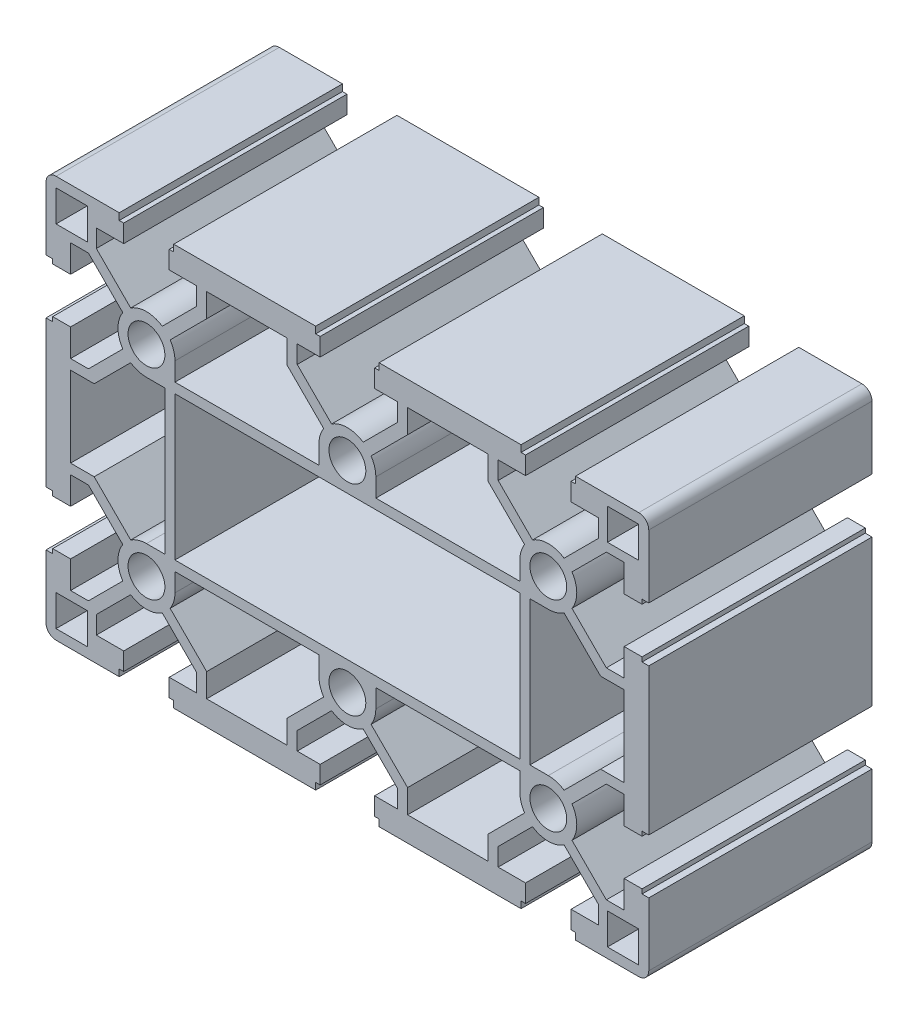
SolidWorks part; units mm, degrees
material "6063-T5"
ref_plane "Ön Düzlem" through (0, 0, 0) normal (0, 0, 1) x (1, 0, 0)
ref_plane "Üst Düzlem" through (0, 0, 0) normal (0, 1, 0) x (1, 0, 0)
ref_plane "Sağ Düzlem" through (0, 0, 0) normal (1, 0, 0) x (0, 0, -1)
sketch "Çizim1" plane through (0, 0, 0) normal (0, 0, 1) x (1, 0, 0)
  line L0 (0, -1000) -> (0, 49000) construction
  line L1 (51.1, 45) -> (65.25, 45)
  line L2 (67.5, 42.75) -> (67.5, 28.6)
  line L3 (67.5, 28.6) -> (66, 28.6)
  line L4 (66, 28.6) -> (66, 27.6)
  line L5 (66, 27.6) -> (62, 27.6)
  line L6 (62, 27.6) -> (62, 33.7322)
  line L7 (-1000, 0) -> (49000, 0) construction
  line L8 (45, -1000) -> (45, 49000) construction
  line L9 (-45, -1000) -> (-45, 49000) construction
  line L10 (-1000, -22.5) -> (49000, -22.5) construction
  line L11 (-1000, 22.5) -> (49000, 22.5) construction
  line L12 (62, 33.7322) -> (58, 33.7322)
  line L13 (45, 22.5) -> (99.0284, 76.5284) construction
  line L14 (50.3042, 26.0364) -> (58, 33.7322)
  line L15 (56.2322, 39.5) -> (56.2322, 35.5)
  line L16 (-45, -18.375) -> (-40.875, -18.375) construction
  line L17 (65.25, 42.75) -> (58.25, 42.75)
  line L18 (65.25, 42.75) -> (65.25, 35.75)
  line L19 (65.25, 35.75) -> (58.25, 35.75)
  line L20 (58.25, 42.75) -> (58.25, 35.75)
  line L21 (48.5364, 27.8042) -> (56.2322, 35.5)
  line L22 (51.1, 45) -> (51.1, 43.5)
  line L23 (51.1, 43.5) -> (50.1, 43.5)
  line L24 (50.1, 43.5) -> (50.1, 39.5)
  line L25 (50.1, 39.5) -> (56.2322, 39.5)
  line L26 (50.3042, 18.9636) -> (58, 11.2678)
  line L27 (62, 11.2678) -> (58, 11.2678)
  line L28 (62, 17.4) -> (62, 11.2678)
  line L29 (66, 17.4) -> (62, 17.4)
  line L30 (66, 16.4) -> (66, 17.4)
  line L31 (67.5, 16.4) -> (66, 16.4)
  line L32 (67.5, -16.4) -> (67.5, 16.4)
  line L33 (-40.875, 22.5) -> (-40.875, 18.375) construction
  line L34 (56.7145, 9.0178) -> (62, 9.0178)
  line L35 (62, 9.0178) -> (62, -9.0178)
  line L36 (48.5364, 17.1958) -> (56.7145, 9.0178)
  line L37 (45, 22.5) -> (11.8849, 55.6151) construction
  line L38 (31.5178, 39.5) -> (13.4822, 39.5)
  line L39 (31.5178, 34.2145) -> (31.5178, 39.5)
  line L40 (39.6958, 26.0364) -> (31.5178, 34.2145)
  line L41 (41.4636, 27.8042) -> (33.7678, 35.5)
  line L42 (33.7678, 39.5) -> (33.7678, 35.5)
  line L43 (39.9, 39.5) -> (33.7678, 39.5)
  line L44 (39.9, 43.5) -> (39.9, 39.5)
  line L45 (38.9, 43.5) -> (39.9, 43.5)
  line L46 (38.9, 45) -> (38.9, 43.5)
  line L47 (7.1, 45) -> (38.9, 45)
  line L48 (22.5, -1000) -> (22.5, 49000) construction
  line L49 (-22.5, -1000) -> (-22.5, 49000) construction
  line L50 (38.625, 22.5) -> (38.625, 18.375)
  line L51 (45, 16.125) -> (40.875, 16.125)
  line L52 (45, 18.375) -> (40.875, 18.375) construction
  line L53 (40.875, 22.5) -> (40.875, 18.375) construction
  line L54 (38.625, 18.375) -> (6.375, 18.375)
  line L55 (38.625, 16.125) -> (38.625, -16.125)
  line L56 (38.625, 16.125) -> (-38.625, 16.125)
  line L57 (40.875, 16.125) -> (40.875, -16.125)
  line L58 (13.4822, 34.2145) -> (13.4822, 39.5)
  line L59 (5.3042, 26.0364) -> (13.4822, 34.2145)
  line L60 (6.375, 22.5) -> (6.375, 18.375)
  line L61 (0, 22.5) -> (33.1151, 55.6151) construction
  line L62 (7.1, 43.5) -> (7.1, 45)
  line L63 (7.1, 43.5) -> (6.1, 43.5)
  line L64 (6.1, 43.5) -> (6.1, 39.5)
  line L65 (6.1, 39.5) -> (11.2322, 39.5)
  line L66 (11.2322, 39.5) -> (11.2322, 35.5)
  line L67 (3.5364, 27.8042) -> (11.2322, 35.5)
  line L68 (40.875, -22.5) -> (40.875, -18.375) construction
  line L69 (-45, 18.375) -> (-40.875, 18.375) construction
  line L70 (-3.5364, 27.8042) -> (-11.2322, 35.5)
  line L71 (-11.2322, 39.5) -> (-11.2322, 35.5)
  line L72 (-6.1, 39.5) -> (-11.2322, 39.5)
  line L73 (-6.1, 43.5) -> (-6.1, 39.5)
  line L74 (-7.1, 43.5) -> (-6.1, 43.5)
  line L75 (-7.1, 45) -> (-7.1, 43.5)
  line L76 (-6.375, 22.5) -> (-6.375, 18.375)
  line L77 (-5.3042, 26.0364) -> (-13.4822, 34.2145)
  line L78 (-13.4822, 34.2145) -> (-13.4822, 39.5)
  line L79 (-40.875, 16.125) -> (-40.875, -16.125)
  line L80 (-38.625, 16.125) -> (-38.625, -16.125)
  line L81 (-38.625, 18.375) -> (-6.375, 18.375)
  line L82 (-45, 16.125) -> (-40.875, 16.125)
  line L83 (-38.625, 22.5) -> (-38.625, 18.375)
  line L84 (-7.1, 45) -> (-38.9, 45)
  line L85 (-38.9, 45) -> (-38.9, 43.5)
  line L86 (-38.9, 43.5) -> (-39.9, 43.5)
  line L87 (-39.9, 43.5) -> (-39.9, 39.5)
  line L88 (-39.9, 39.5) -> (-33.7678, 39.5)
  line L89 (-33.7678, 39.5) -> (-33.7678, 35.5)
  line L90 (-41.4636, 27.8042) -> (-33.7678, 35.5)
  line L91 (-39.6958, 26.0364) -> (-31.5178, 34.2145)
  line L92 (-31.5178, 34.2145) -> (-31.5178, 39.5)
  line L93 (-31.5178, 39.5) -> (-13.4822, 39.5)
  line L94 (-48.5364, 17.1958) -> (-56.7145, 9.0178)
  line L95 (-62, 9.0178) -> (-62, -9.0178)
  line L96 (-56.7145, 9.0178) -> (-62, 9.0178)
  line L97 (-67.5, -16.4) -> (-67.5, 16.4)
  line L98 (-67.5, 16.4) -> (-66, 16.4)
  line L99 (-66, 16.4) -> (-66, 17.4)
  line L100 (-66, 17.4) -> (-62, 17.4)
  line L101 (-62, 17.4) -> (-62, 11.2678)
  line L102 (-62, 11.2678) -> (-58, 11.2678)
  line L103 (-50.3042, 18.9636) -> (-58, 11.2678)
  line L104 (-50.1, 39.5) -> (-56.2322, 39.5)
  line L105 (-50.1, 43.5) -> (-50.1, 39.5)
  line L106 (-51.1, 43.5) -> (-50.1, 43.5)
  line L107 (-51.1, 45) -> (-51.1, 43.5)
  line L108 (-48.5364, 27.8042) -> (-56.2322, 35.5)
  line L109 (-58.25, 42.75) -> (-58.25, 35.75)
  line L110 (-65.25, 35.75) -> (-58.25, 35.75)
  line L111 (-65.25, 42.75) -> (-65.25, 35.75)
  line L112 (-65.25, 42.75) -> (-58.25, 42.75)
  line L113 (-56.2322, 39.5) -> (-56.2322, 35.5)
  line L114 (-50.3042, 26.0364) -> (-58, 33.7322)
  line L115 (-62, 33.7322) -> (-58, 33.7322)
  line L116 (-62, 27.6) -> (-62, 33.7322)
  line L117 (-66, 27.6) -> (-62, 27.6)
  line L118 (-66, 28.6) -> (-66, 27.6)
  line L119 (-67.5, 28.6) -> (-66, 28.6)
  line L120 (-67.5, 42.75) -> (-67.5, 28.6)
  line L121 (-51.1, 45) -> (-65.25, 45)
  line L122 (45, -18.375) -> (40.875, -18.375) construction
  line L123 (-40.875, -22.5) -> (-40.875, -18.375) construction
  line L124 (-51.1, -45) -> (-65.25, -45)
  line L125 (-67.5, -42.75) -> (-67.5, -28.6)
  line L126 (-67.5, -28.6) -> (-66, -28.6)
  line L127 (-66, -28.6) -> (-66, -27.6)
  line L128 (-66, -27.6) -> (-62, -27.6)
  line L129 (-62, -27.6) -> (-62, -33.7322)
  line L130 (-62, -33.7322) -> (-58, -33.7322)
  line L131 (-50.3042, -26.0364) -> (-58, -33.7322)
  line L132 (-56.2322, -39.5) -> (-56.2322, -35.5)
  line L133 (-65.25, -42.75) -> (-58.25, -42.75)
  line L134 (-65.25, -42.75) -> (-65.25, -35.75)
  line L135 (-65.25, -35.75) -> (-58.25, -35.75)
  line L136 (-58.25, -42.75) -> (-58.25, -35.75)
  line L137 (-48.5364, -27.8042) -> (-56.2322, -35.5)
  line L138 (-51.1, -45) -> (-51.1, -43.5)
  line L139 (-51.1, -43.5) -> (-50.1, -43.5)
  line L140 (-50.1, -43.5) -> (-50.1, -39.5)
  line L141 (-50.1, -39.5) -> (-56.2322, -39.5)
  line L142 (-50.3042, -18.9636) -> (-58, -11.2678)
  line L143 (-62, -11.2678) -> (-58, -11.2678)
  line L144 (-62, -17.4) -> (-62, -11.2678)
  line L145 (-66, -17.4) -> (-62, -17.4)
  line L146 (-66, -16.4) -> (-66, -17.4)
  line L147 (-67.5, -16.4) -> (-66, -16.4)
  line L148 (-56.7145, -9.0178) -> (-62, -9.0178)
  line L149 (-48.5364, -17.1958) -> (-56.7145, -9.0178)
  line L150 (-31.5178, -39.5) -> (-13.4822, -39.5)
  line L151 (-31.5178, -34.2145) -> (-31.5178, -39.5)
  line L152 (-39.6958, -26.0364) -> (-31.5178, -34.2145)
  line L153 (-41.4636, -27.8042) -> (-33.7678, -35.5)
  line L154 (-33.7678, -39.5) -> (-33.7678, -35.5)
  line L155 (-39.9, -39.5) -> (-33.7678, -39.5)
  line L156 (-39.9, -43.5) -> (-39.9, -39.5)
  line L157 (-38.9, -43.5) -> (-39.9, -43.5)
  line L158 (-38.9, -45) -> (-38.9, -43.5)
  line L159 (-7.1, -45) -> (-38.9, -45)
  line L160 (-38.625, -22.5) -> (-38.625, -18.375)
  line L161 (-45, -16.125) -> (-40.875, -16.125)
  line L162 (-38.625, -18.375) -> (-6.375, -18.375)
  line L163 (-13.4822, -34.2145) -> (-13.4822, -39.5)
  line L164 (-5.3042, -26.0364) -> (-13.4822, -34.2145)
  line L165 (-6.375, -22.5) -> (-6.375, -18.375)
  line L166 (-7.1, -45) -> (-7.1, -43.5)
  line L167 (-7.1, -43.5) -> (-6.1, -43.5)
  line L168 (-6.1, -43.5) -> (-6.1, -39.5)
  line L169 (-6.1, -39.5) -> (-11.2322, -39.5)
  line L170 (-11.2322, -39.5) -> (-11.2322, -35.5)
  line L171 (-3.5364, -27.8042) -> (-11.2322, -35.5)
  line L172 (3.5364, -27.8042) -> (11.2322, -35.5)
  line L173 (11.2322, -39.5) -> (11.2322, -35.5)
  line L174 (6.1, -39.5) -> (11.2322, -39.5)
  line L175 (6.1, -43.5) -> (6.1, -39.5)
  line L176 (7.1, -43.5) -> (6.1, -43.5)
  line L177 (7.1, -45) -> (7.1, -43.5)
  line L178 (6.375, -22.5) -> (6.375, -18.375)
  line L179 (5.3042, -26.0364) -> (13.4822, -34.2145)
  line L180 (13.4822, -34.2145) -> (13.4822, -39.5)
  line L181 (38.625, -16.125) -> (-38.625, -16.125)
  line L182 (38.625, -18.375) -> (6.375, -18.375)
  line L183 (45, -16.125) -> (40.875, -16.125)
  line L184 (38.625, -22.5) -> (38.625, -18.375)
  line L185 (7.1, -45) -> (38.9, -45)
  line L186 (38.9, -45) -> (38.9, -43.5)
  line L187 (38.9, -43.5) -> (39.9, -43.5)
  line L188 (39.9, -43.5) -> (39.9, -39.5)
  line L189 (39.9, -39.5) -> (33.7678, -39.5)
  line L190 (33.7678, -39.5) -> (33.7678, -35.5)
  line L191 (41.4636, -27.8042) -> (33.7678, -35.5)
  line L192 (39.6958, -26.0364) -> (31.5178, -34.2145)
  line L193 (31.5178, -34.2145) -> (31.5178, -39.5)
  line L194 (31.5178, -39.5) -> (13.4822, -39.5)
  line L195 (48.5364, -17.1958) -> (56.7145, -9.0178)
  line L196 (56.7145, -9.0178) -> (62, -9.0178)
  line L197 (67.5, -16.4) -> (66, -16.4)
  line L198 (66, -16.4) -> (66, -17.4)
  line L199 (66, -17.4) -> (62, -17.4)
  line L200 (62, -17.4) -> (62, -11.2678)
  line L201 (62, -11.2678) -> (58, -11.2678)
  line L202 (50.3042, -18.9636) -> (58, -11.2678)
  line L203 (50.1, -39.5) -> (56.2322, -39.5)
  line L204 (50.1, -43.5) -> (50.1, -39.5)
  line L205 (51.1, -43.5) -> (50.1, -43.5)
  line L206 (51.1, -45) -> (51.1, -43.5)
  line L207 (48.5364, -27.8042) -> (56.2322, -35.5)
  line L208 (58.25, -42.75) -> (58.25, -35.75)
  line L209 (65.25, -35.75) -> (58.25, -35.75)
  line L210 (65.25, -42.75) -> (65.25, -35.75)
  line L211 (65.25, -42.75) -> (58.25, -42.75)
  line L212 (56.2322, -39.5) -> (56.2322, -35.5)
  line L213 (50.3042, -26.0364) -> (58, -33.7322)
  line L214 (62, -33.7322) -> (58, -33.7322)
  line L215 (62, -27.6) -> (62, -33.7322)
  line L216 (66, -27.6) -> (62, -27.6)
  line L217 (66, -28.6) -> (66, -27.6)
  line L218 (67.5, -28.6) -> (66, -28.6)
  line L219 (67.5, -42.75) -> (67.5, -28.6)
  line L220 (51.1, -45) -> (65.25, -45)
  arc A0 (39.6958, 26.0364) -> (38.625, 22.5) centre (45, 22.5) ccw
  circle A1 centre (45, 22.5) radius 4.125
  arc A2 (48.5364, 27.8042) -> (41.4636, 27.8042) centre (45, 22.5) ccw
  arc A3 (-39.6958, -26.0364) -> (-38.625, -22.5) centre (-45, -22.5) ccw
  arc A4 (50.3042, 18.9636) -> (50.3042, 26.0364) centre (45, 22.5) ccw
  arc A5 (45, 16.125) -> (48.5364, 17.1958) centre (45, 22.5) ccw
  arc A6 (5.3042, 26.0364) -> (6.375, 22.5) centre (0, 22.5) cw
  arc A7 (-3.5364, 27.8042) -> (3.5364, 27.8042) centre (0, 22.5) cw
  circle A8 centre (0, 22.5) radius 4.125
  arc A9 (65.25, 45) -> (67.5, 42.75) centre (65.25, 42.75) cw
  arc A10 (-65.25, 45) -> (-67.5, 42.75) centre (-65.25, 42.75) ccw
  arc A11 (-5.3042, 26.0364) -> (-6.375, 22.5) centre (0, 22.5) ccw
  arc A12 (-45, 16.125) -> (-48.5364, 17.1958) centre (-45, 22.5) cw
  arc A13 (-50.3042, 18.9636) -> (-50.3042, 26.0364) centre (-45, 22.5) cw
  arc A14 (-48.5364, 27.8042) -> (-41.4636, 27.8042) centre (-45, 22.5) cw
  circle A15 centre (-45, 22.5) radius 4.125
  arc A16 (-39.6958, 26.0364) -> (-38.625, 22.5) centre (-45, 22.5) cw
  circle A17 centre (-45, -22.5) radius 4.125
  arc A18 (-48.5364, -27.8042) -> (-41.4636, -27.8042) centre (-45, -22.5) ccw
  arc A19 (-50.3042, -18.9636) -> (-50.3042, -26.0364) centre (-45, -22.5) ccw
  arc A20 (-45, -16.125) -> (-48.5364, -17.1958) centre (-45, -22.5) ccw
  arc A21 (-5.3042, -26.0364) -> (-6.375, -22.5) centre (0, -22.5) cw
  arc A22 (-65.25, -45) -> (-67.5, -42.75) centre (-65.25, -42.75) cw
  arc A23 (65.25, -45) -> (67.5, -42.75) centre (65.25, -42.75) ccw
  circle A24 centre (0, -22.5) radius 4.125
  arc A25 (-3.5364, -27.8042) -> (3.5364, -27.8042) centre (0, -22.5) ccw
  arc A26 (5.3042, -26.0364) -> (6.375, -22.5) centre (0, -22.5) ccw
  arc A27 (45, -16.125) -> (48.5364, -17.1958) centre (45, -22.5) cw
  arc A28 (50.3042, -18.9636) -> (50.3042, -26.0364) centre (45, -22.5) cw
  arc A29 (48.5364, -27.8042) -> (41.4636, -27.8042) centre (45, -22.5) cw
  circle A30 centre (45, -22.5) radius 4.125
  arc A31 (39.6958, -26.0364) -> (38.625, -22.5) centre (45, -22.5) cw
  point P0 (0, 0)
  point P24 (45.8839, 21.6161)
  point P25 (78.999, 54.7312)
  point P33 (51.375, 22.5)
  point P40 (67.5, 45)
  point P85 (67.5, 45)
  point P101 (-40.875, 0)
  point P135 (0, 16.125)
  point P233 (-67.5, 0)
  point P235 (-62, 0)
  point P249 (-38.625, 0)
  point P265 (40.875, 0)
  point P266 (38.625, 0)
  point P277 (62, 0)
  point P278 (67.5, 0)
  point P298 (0, -16.125)
  point P299 (67.5, -45)
  dimension "D10" = 2.25
  dimension "D16" = 22.5
  dimension "D17" = 8.25
  dimension "D18" = 5.1
  dimension "D3" = 8.25
  dimension "D29" = 1.5
  dimension "D31" = 2.25
  dimension "D9" = 2.25
  dimension "D1" = 5.1
  dimension "D2" = 1
  dimension "D7" = 1.5
  dimension "D8" = 22.5
  dimension "D12" = 5.5
  dimension "D13" = 4
  dimension "D14" = 1.25
  dimension "D15" = 7
  dimension "D6" = 22.5
  dimension "D19" = 1.5
  dimension "D20" = 1
  dimension "D21" = 22.5
  dimension "D24" = 5.1
  dimension "D25" = 1
  dimension "D26" = 1.5
  dimension "D27" = 1.25
  dimension "D28" = 2.25
  dimension "D30" = 22.5
  dimension "D4" = 22.5
  dimension "D5" = 1.25
  dimension "D11" = 1.25
  dimension "D22" = 6.1
  dimension "D23" = 1
extrude "Yükseklik-Ekstrüzyon1" add sketch "Çizim1" along normal mid plane 50
